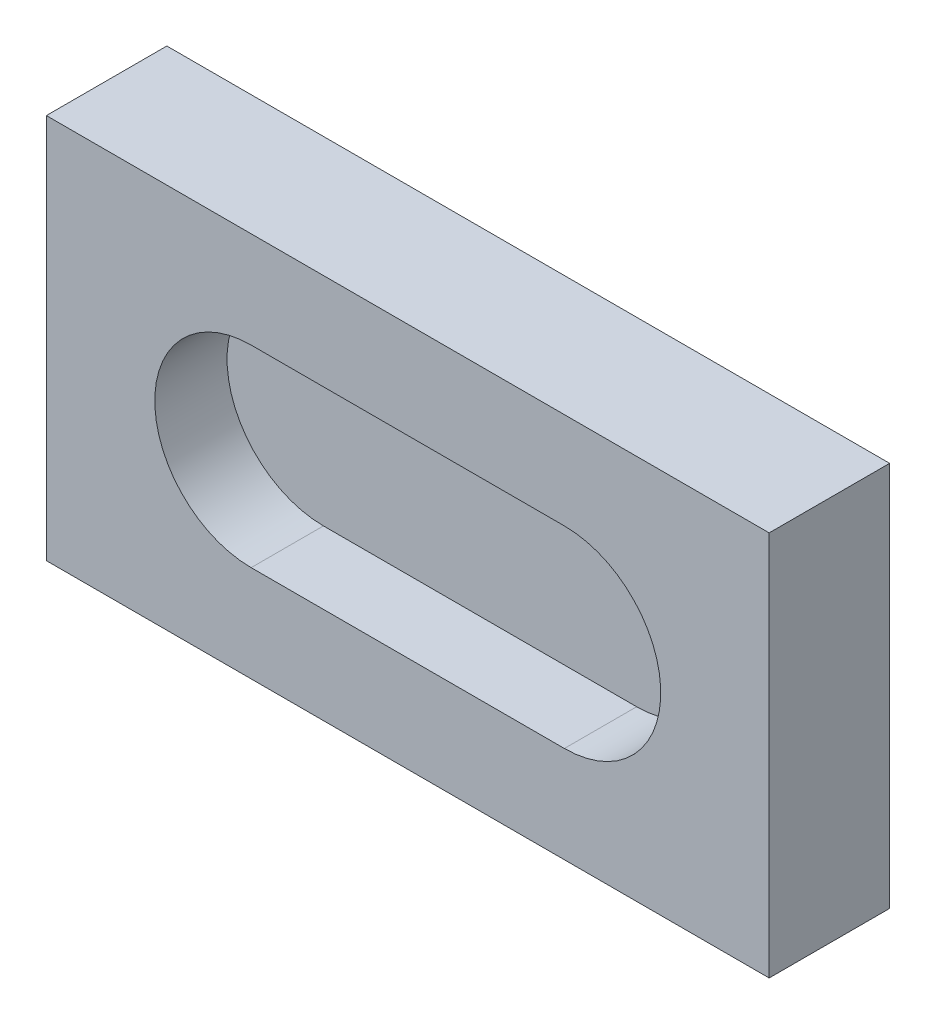
SolidWorks part; units mm, degrees
ref_plane "前视基准面" through (0, 0, 0) normal (0, 0, 1) x (1, 0, 0)
ref_plane "上视基准面" through (0, 0, 0) normal (0, 1, 0) x (1, 0, 0)
ref_plane "右视基准面" through (0, 0, 0) normal (1, 0, 0) x (0, 0, -1)
other "Configuration Table"
sketch "草图1" plane through (0, 0, 0) normal (0, 1, 0) x (1, 0, 0)
  line L1 (-75, 40) -> (75, 40)
  line L2 (-75, 40) -> (-75, -40)
  line L3 (-75, -40) -> (75, -40)
  line L4 (75, 40) -> (75, -40)
  line L5 (-75, 40) -> (75, -40) construction
  line L6 (-75, -40) -> (75, 40) construction
  point P0 (0, 0)
  dimension "D1" = 150
  dimension "D2" = 80
extrude "凸台-拉伸1" add sketch "草图1" along normal blind 25
sketch "草图2" plane through (0, 25, 0) normal (0, 1, 0) x (1, 0, 0)
  line L0 (-32.5, 0) -> (32.5, 0) construction
  line L1 (-32.5, 20) -> (32.5, 20)
  line L2 (-32.5, -20) -> (32.5, -20)
  arc A0 (-32.5, 20) -> (-32.5, -20) centre (-32.5, 0) ccw
  arc A1 (32.5, -20) -> (32.5, 20) centre (32.5, 0) ccw
  point P2 (0, 0)
  dimension "D1" = 20
  dimension "D2" = 65
extrude "切除-拉伸1" cut sketch "草图2" against normal blind 15
move or copy body "实体-移动/复制1" bodies to move or copy 107 copy no rotation origin (0, 12.5, 0) rotation axis (1, 0, 0) rotation angle 90
